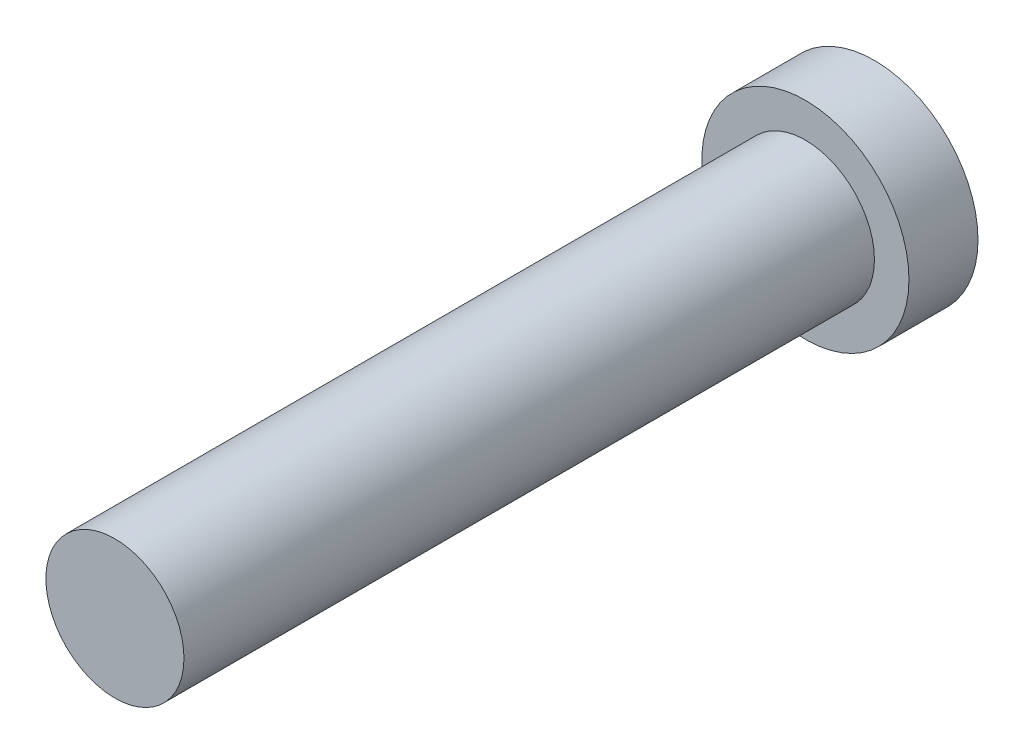
SolidWorks part; units mm, degrees
ref_plane "Front Plane" through (0, 0, 0) normal (0, 0, 1) x (1, 0, 0)
ref_plane "Top Plane" through (0, 0, 0) normal (0, 1, 0) x (1, 0, 0)
ref_plane "Right Plane" through (0, 0, 0) normal (1, 0, 0) x (0, 0, -1)
sketch "Sketch1" plane through (0, 0, 0) normal (0, 0, 1) x (1, 0, 0)
  circle A0 centre (0, 0) radius 3.81
  dimension "D1" = 7.62
extrude "Boss-Extrude1" add sketch "Sketch1" along normal blind 2.54
sketch "Sketch2" plane through (0, 0, 2.54) normal (0, 0, 1) x (1, 0, 0)
  circle A0 centre (0, 0) radius 2.54
  dimension "D1" = 5.08
extrude "Boss-Extrude2" add sketch "Sketch2" along normal blind 25.4
